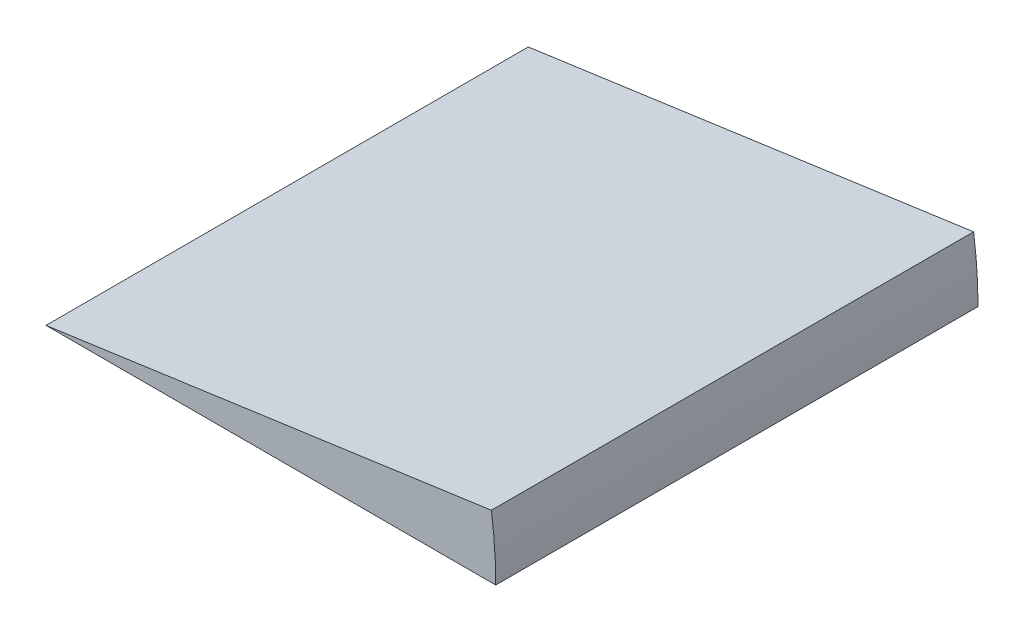
SolidWorks part; units mm, degrees
ref_plane "Front Plane" through (0, 0, 0) normal (0, 0, 1) x (1, 0, 0)
ref_plane "Top Plane" through (0, 0, 0) normal (0, 1, 0) x (1, 0, 0)
ref_plane "Right Plane" through (0, 0, 0) normal (1, 0, 0) x (0, 0, -1)
sketch "Sketch1" plane through (0, 0, 0) normal (0, 1, 0) x (1, 0, 0)
  line L1 (-54.483, -58.42) -> (54.483, -58.42)
  line L2 (-54.483, -58.42) -> (-54.483, 58.42)
  line L3 (-54.483, 58.42) -> (54.483, 58.42)
  line L4 (54.483, -58.42) -> (54.483, 58.42)
  line L5 (-54.483, -58.42) -> (54.483, 58.42) construction
  line L6 (-54.483, 58.42) -> (54.483, -58.42) construction
  point P0 (0, 0)
  dimension "D1" = 108.966
  dimension "D2" = 116.84
revolve "Revolve1" add sketch "Sketch1" angle 8 about L2
